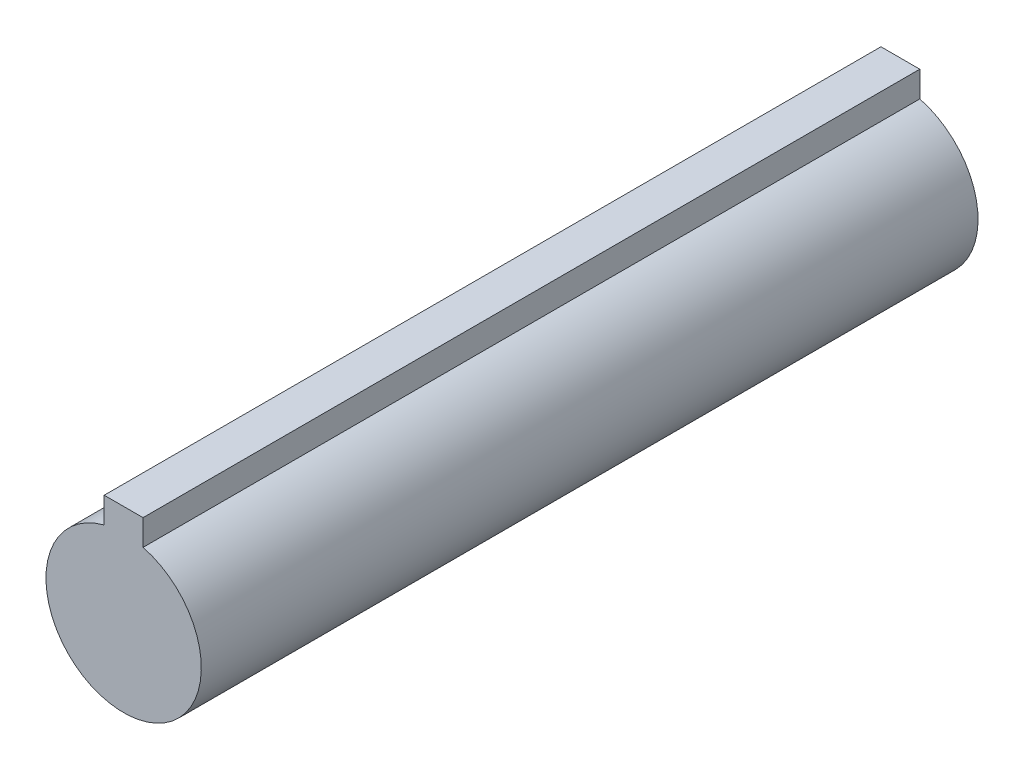
SolidWorks part; units mm, degrees
ref_plane "Front Plane" through (0, 0, 0) normal (0, 0, 1) x (1, 0, 0)
ref_plane "Top Plane" through (0, 0, 0) normal (0, 1, 0) x (1, 0, 0)
ref_plane "Right Plane" through (0, 0, 0) normal (1, 0, 0) x (0, 0, -1)
sketch "Sketch1" plane through (0, 0, 0) normal (0, 0, 1) x (1, 0, 0)
  line L2 (2.5, 9.6825) -> (2.5, 13)
  line L3 (-2.5, 9.6825) -> (-2.5, 13)
  line L4 (-2.5, 13) -> (2.5, 13)
  arc A0 (-2.5, 9.6825) -> (2.5, 9.6825) centre (0, 0) ccw
  point P5 (0, 0)
extrude "Boss-Extrude1" add sketch "Sketch1" along normal mid plane 100
